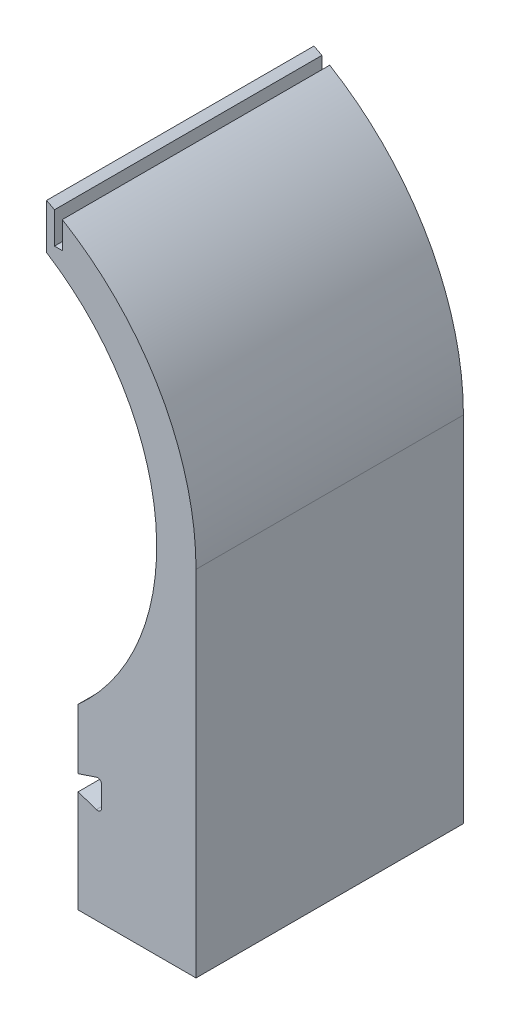
SolidWorks part; units mm, degrees
material "201 Annealed Stainless Steel (SS)"
ref_plane "Front Plane" through (0, 0, 0) normal (0, 0, 1) x (1, 0, 0)
ref_plane "Top Plane" through (0, 0, 0) normal (0, 1, 0) x (1, 0, 0)
ref_plane "Right Plane" through (0, 0, 0) normal (1, 0, 0) x (0, 0, -1)
sketch "Sketch2" plane through (0, 0, 0) normal (0, 0, 1) x (1, 0, 0)
  line L0 (-81.7487, 0) -> (129.7647, 0) construction
  line L1 (0, 82.2046) -> (0, -175) construction
  line L2 (80, 0) -> (80, 108.9269) construction
  line L3 (100, -111.8034) -> (100, -150)
  line L5 (175, 0) -> (175, -225)
  line L6 (175, -225) -> (100, -225)
  line L7 (80, 155.6438) -> (80, 126.8858)
  line L8 (0, -175) -> (0, -225) construction
  line L9 (0, -225) -> (111.0903, -225) construction
  line L10 (-100, -111.8034) -> (100, -111.8034) construction
  line L11 (85, 152.9706) -> (85, 132.9706)
  line L12 (85, 132.9706) -> (90, 132.9706)
  line L13 (90, 132.9706) -> (90, 150.0833)
  line L14 (0, -150) -> (175, -150) construction
  line L15 (100, -150) -> (111.7094, -146.0969)
  line L16 (115, -148.4686) -> (115, -161.5314)
  line L17 (111.7094, -163.9031) -> (100, -160)
  line L18 (100, -160) -> (100, -225)
  line L19 (100, -150) -> (100, -160) construction
  line L20 (100, -155) -> (115, -155) construction
  circle A0 centre (0, 0) radius 150 construction
  circle A1 centre (0, 0) radius 175 construction
  arc A2 (80, 126.8858) -> (100, -111.8034) centre (0, 0) cw
  arc A3 (175, 0) -> (90, 150.0833) centre (0, 0) ccw
  arc A4 (85, 152.9706) -> (80, 155.6438) centre (0, 0) ccw
  arc A5 (111.7094, -163.9031) -> (115, -161.5314) centre (112.5, -161.5314) ccw
  arc A6 (115, -148.4686) -> (111.7094, -146.0969) centre (112.5, -148.4686) ccw
  point P33 (115, -165)
  point P36 (115, -145)
  dimension "D1" = 300
  dimension "D2" = 350
  dimension "D5" = 50
  dimension "D12" = 2.5
  dimension "D3" = 90
  dimension "D4" = 20
  dimension "D6" = 200
  dimension "D7" = 5
  dimension "D8" = 5
  dimension "D9" = 10
  dimension "D10" = 20
  dimension "D11" = 15
extrude "Inner Ring - Right Side" add sketch "Sketch2" along normal blind 170
